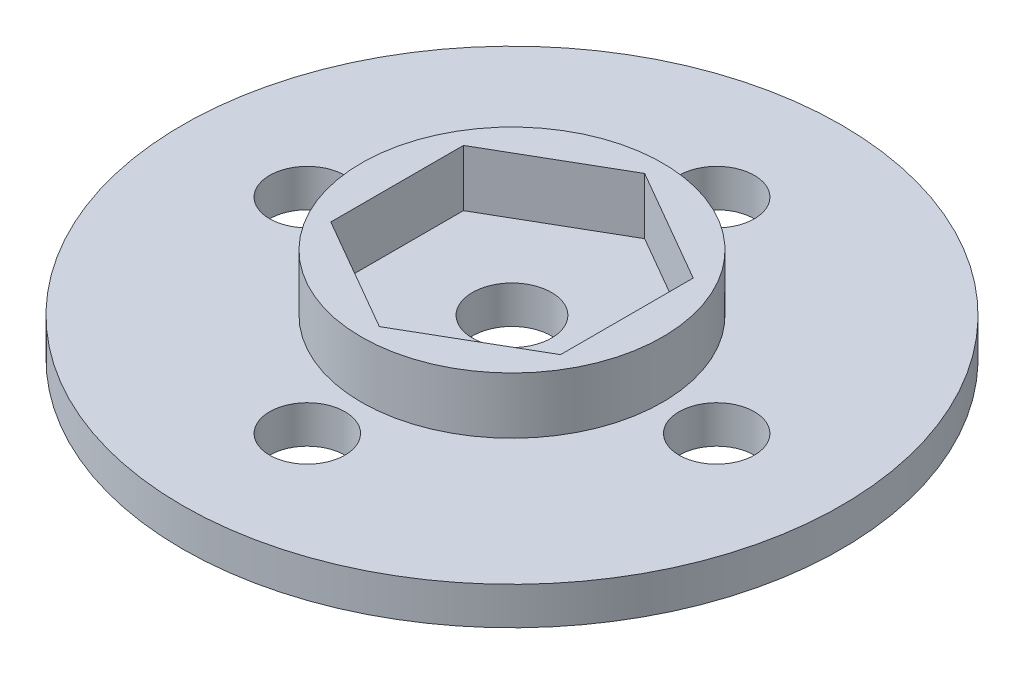
SolidWorks part; units mm, degrees
ref_plane "Front Plane" through (0, 0, 0) normal (0, 0, 1) x (1, 0, 0)
ref_plane "Top Plane" through (0, 0, 0) normal (0, 1, 0) x (1, 0, 0)
ref_plane "Right Plane" through (0, 0, 0) normal (1, 0, 0) x (0, 0, -1)
sketch "Sketch4" plane through (0, 0, 0) normal (0, 1, 0) x (1, 0, 0)
  line L0 (0, 0) -> (10.87, 0)
  circle A0 centre (0, 0) radius 17.5
  circle A1 centre (10.87, 0) radius 2
  circle A2 centre (0, -10.87) radius 2
  circle A3 centre (-10.87, 0) radius 2
  circle A4 centre (0, 10.87) radius 2
  dimension "D1" = 35
  dimension "D2" = 10.87
  dimension "D3" = 4
  dimension "D4" = 4
extrude "Boss-Extrude1" add sketch "Sketch4" along normal blind 2
sketch "Sketch5" plane through (0, 0, 0) normal (0, 1, 0) x (-1, 0, 0)
  line L7 (0, -6.9282) -> (6, -3.4641)
  line L8 (6, -3.4641) -> (6, 3.4641)
  line L9 (6, 3.4641) -> (0, 6.9282)
  line L10 (0, 6.9282) -> (-6, 3.4641)
  line L11 (-6, 3.4641) -> (-6, -3.4641)
  line L12 (-6, -3.4641) -> (0, -6.9282)
  line L13 (26.5421, 3.4641) -> (10.271, 24.7182)
  line L14 (10.271, 24.7182) -> (-16.271, 21.2541)
  line L15 (-16.271, 21.2541) -> (-26.5421, -3.4641)
  line L16 (-26.5421, -3.4641) -> (-10.271, -24.7182)
  line L17 (-10.271, -24.7182) -> (16.271, -21.2541)
  line L18 (16.271, -21.2541) -> (26.5421, 3.4641)
  line L19 (0, -7.0437) -> (6.1, -3.5218)
  line L20 (6.1, -3.5218) -> (6.1, 3.5218)
  line L21 (6.1, 3.5218) -> (0, 7.0437)
  line L22 (0, 7.0437) -> (-6.1, 3.5218)
  line L23 (-6.1, 3.5218) -> (-6.1, -3.5218)
  line L24 (-6.1, -3.5218) -> (0, -7.0437)
  circle A1 centre (0, 0) radius 6 construction
  circle A2 centre (0, 0) radius 8
  circle A3 centre (0, 0) radius 23.1811 construction
  circle A4 centre (0, 0) radius 6.1 construction
  dimension "D1" = 12
  dimension "D2" = 12.2
  dimension "D3" = 16
extrude "Boss-Extrude2" add sketch "Sketch5" along normal blind 5 contours A2 L24 L23 L22 L21 L20 L19
sketch "Sketch6" plane through (0, 0, 0) normal (0, 1, 0) x (1, 0, 0)
  circle A0 centre (0, 0) radius 2.1
  dimension "D1" = 4.2
extrude "Cut-Extrude1" cut sketch "Sketch6" against normal through all and the other way through all
